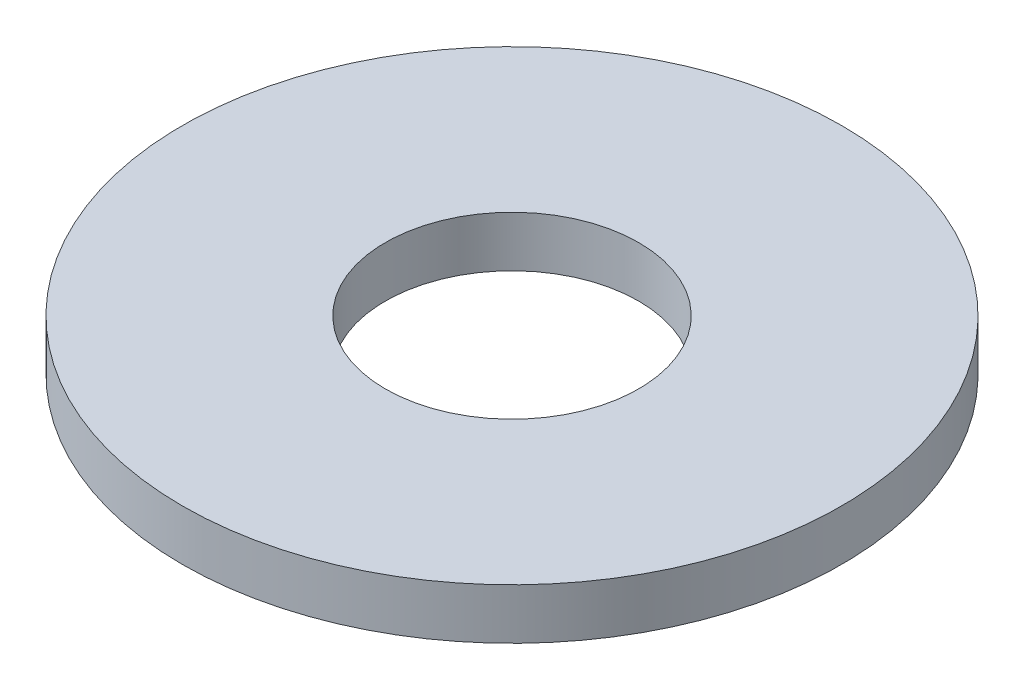
SolidWorks part; units mm, degrees
material "1060 Alloy"
ref_plane "Front Plane" through (0, 0, 0) normal (0, 0, 1) x (1, 0, 0)
ref_plane "Top Plane" through (0, 0, 0) normal (0, 1, 0) x (1, 0, 0)
ref_plane "Right Plane" through (0, 0, 0) normal (1, 0, 0) x (0, 0, -1)
sketch "Sketch1" plane through (0, 0, 0) normal (0, 1, 0) x (1, 0, 0)
  line L1 (2.7424, -4.75) -> (5.4848, 0)
  line L2 (5.4848, 0) -> (2.7424, 4.75)
  line L3 (2.7424, 4.75) -> (-2.7424, 4.75)
  line L4 (-2.7424, 4.75) -> (-5.4848, 0)
  line L5 (-5.4848, 0) -> (-2.7424, -4.75)
  line L6 (-2.7424, -4.75) -> (2.7424, -4.75)
  circle A0 centre (0, 0) radius 4.75 construction
  circle A2 centre (0, 0) radius 6.5
  circle A3 centre (0, 0) radius 2.5
  point P12 (0, 0)
  dimension "D2" = 5
  dimension "D1" = 9.5
  dimension "D3" = 13
extrude "Boss-Extrude1" add sketch "Sketch1" against normal blind 1 contours A2 L6 L5 L4 L3 L2 L1 | L5 L6 L1 L2 L3 L4 A3
